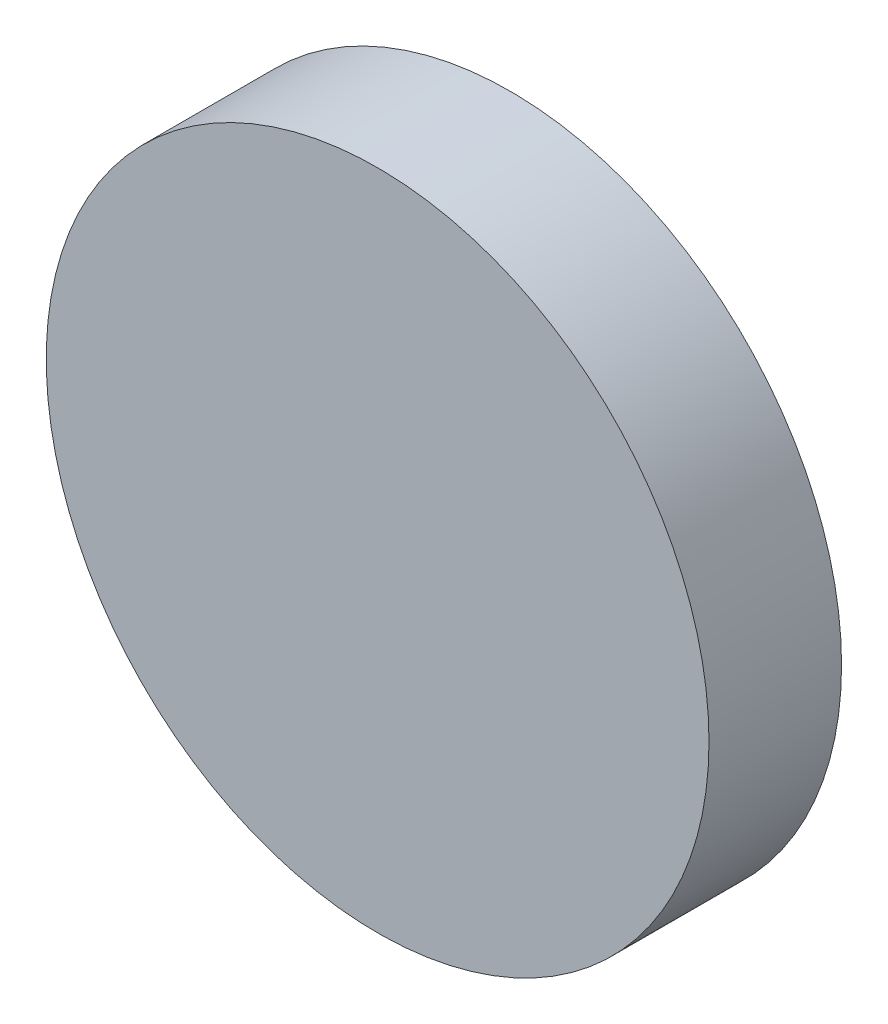
SolidWorks part; units mm, degrees
ref_plane "前视基准面" through (0, 0, 0) normal (0, 0, 1) x (1, 0, 0)
ref_plane "上视基准面" through (0, 0, 0) normal (0, 1, 0) x (1, 0, 0)
ref_plane "右视基准面" through (0, 0, 0) normal (1, 0, 0) x (0, 0, -1)
sketch "草图1" plane through (0, 0, 0) normal (0, 0, 1) x (1, 0, 0)
  circle A0 centre (0, 0) radius 10
  dimension "D1" = 20
extrude "凸台-拉伸1" add sketch "草图1" along normal blind 4
